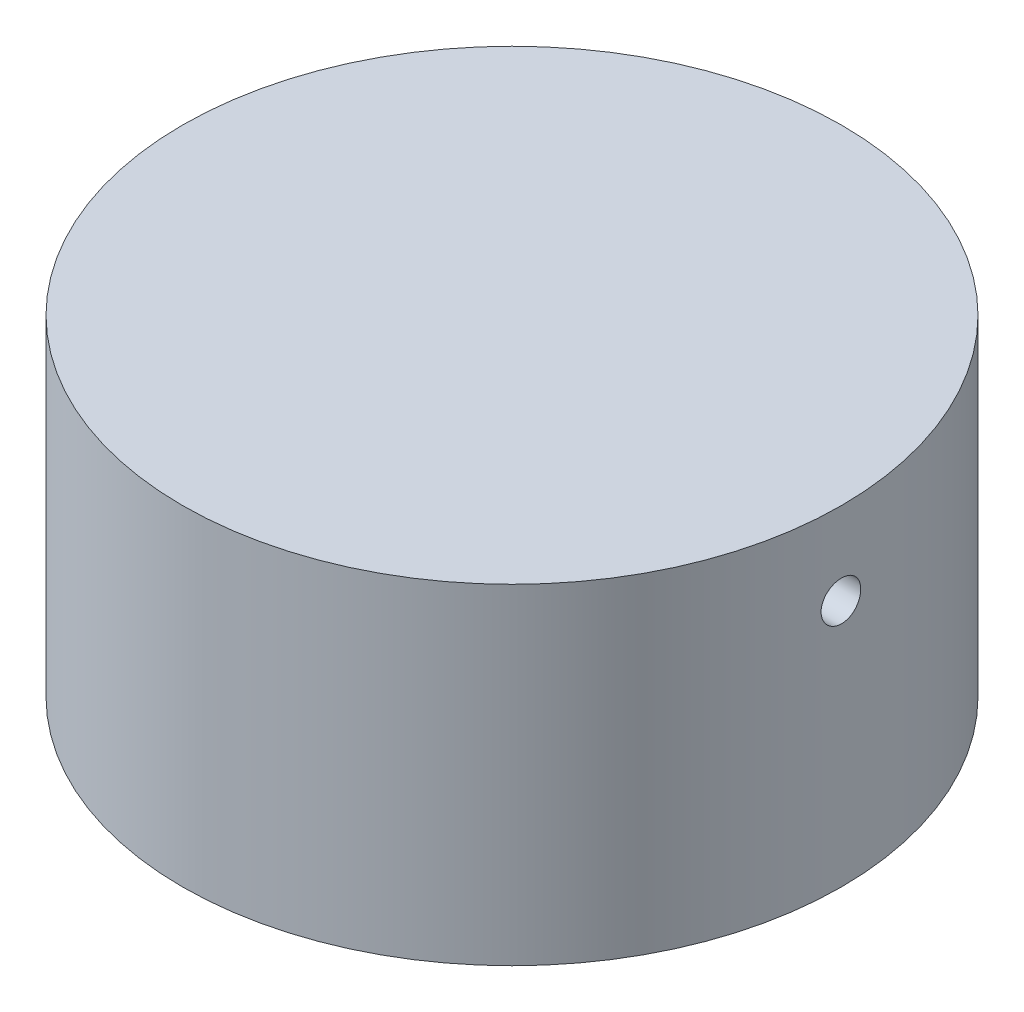
SolidWorks part; units mm, degrees
ref_plane "Front Plane" through (0, 0, 0) normal (0, 0, 1) x (1, 0, 0)
ref_plane "Top Plane" through (0, 0, 0) normal (0, 1, 0) x (1, 0, 0)
ref_plane "Right Plane" through (0, 0, 0) normal (1, 0, 0) x (0, 0, -1)
sketch "Sketch1" plane through (0, 0, 0) normal (0, 1, 0) x (1, 0, 0)
  circle A0 centre (0, 0) radius 19.95
extrude "Boss-Extrude1" add sketch "Sketch1" along normal blind 20
sketch "Sketch5" plane through (0, 0, 0) normal (0, 0, 1) x (1, 0, 0)
  line L0 (0, 0) -> (0, 10)
  line L1 (5, 15) -> (19.95, 15)
  line L2 (19.95, 0) -> (19.95, 20) construction
  arc A0 (0, 10) -> (5, 15) centre (5, 10) cw
  dimension "D1" = 5
sketch "Sketch6" plane through (0, 0, 0) normal (0, -1, 0) x (-1, 0, 0)
  circle A0 centre (0, 0) radius 1.2
sweep "Cut-Sweep2" cut profiles "Sketch6" path "Sketch5"
ref_plane "Plane1" through (19.95, 0, 0) normal (1, 0, 0) x (0, 0, -1)
sketch "Sketch12" plane through (0, 0, 0) normal (0, -1, 0) x (-1, 0, 0)
  circle A0 centre (0, 0) radius 1.9
extrude "Boss-Extrude2" add sketch "Sketch12" along normal blind 10
sketch "Sketch13" plane through (0, -10, 0) normal (0, -1, 0) x (-1, 0, 0)
  circle A0 centre (0, 0) radius 0.9
extrude "Cut-Extrude1" cut sketch "Sketch13" against normal blind 10
sketch "Sketch14" plane through (0, 0, 0) normal (0, -1, 0) x (-1, 0, 0)
  circle A0 centre (-15, 0) radius 1.65
  circle A1 centre (0, 15) radius 1.65
  circle A2 centre (0, -15) radius 1.65
  circle A3 centre (15, 0) radius 1.65
  point P8 (0, 0)
extrude "Cut-Extrude2" cut sketch "Sketch14" against normal blind 5.5
